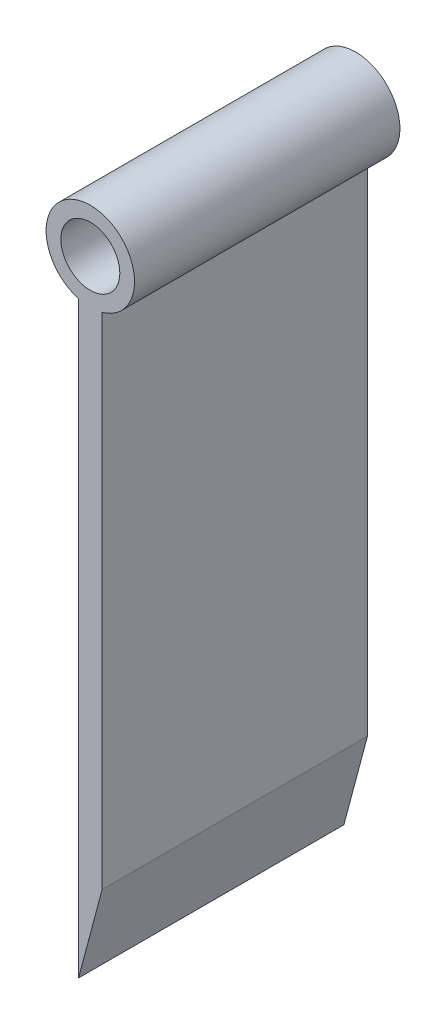
SolidWorks part; units mm, degrees
ref_plane "Alzado" through (0, 0, 0) normal (0, 0, 1) x (1, 0, 0)
ref_plane "Planta" through (0, 0, 0) normal (0, 1, 0) x (1, 0, 0)
ref_plane "Vista lateral" through (0, 0, 0) normal (1, 0, 0) x (0, 0, -1)
sketch "Croquis1" plane through (0, 0, 0) normal (0, 0, 1) x (1, 0, 0)
  line L0 (0, 0) -> (0, 49.8858)
  line L2 (2, 49.8858) -> (2, 7.5)
  line L3 (2, 7.5) -> (0, 0)
  circle A1 centre (1, 53.5) radius 2.5
  circle A2 centre (1, 53.5) radius 3.75
  dimension "D4" = 5
  dimension "D5" = 7.5
extrude "Saliente-Extruir1" add sketch "Croquis1" along normal blind 22.5 contours A2 A1 | A2 L0 L3 L2
